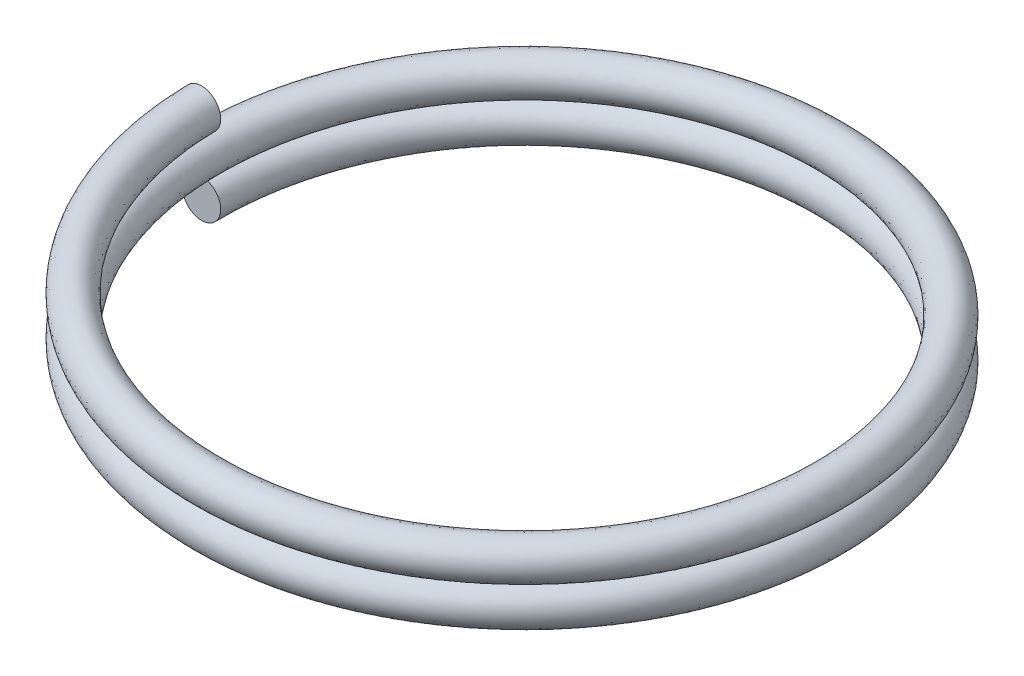
SolidWorks part; units mm, degrees
material "Stainless Steel (ferritic)"
ref_plane "Front Plane" through (0, 0, 0) normal (0, 0, 1) x (1, 0, 0)
ref_plane "Top Plane" through (0, 0, 0) normal (0, 1, 0) x (1, 0, 0)
ref_plane "Right Plane" through (0, 0, 0) normal (1, 0, 0) x (0, 0, -1)
sketch "Sketch1" plane through (0, 0, 0) normal (0, 1, 0) x (1, 0, 0)
  circle A0 centre (0, 0) radius 4.1275
  dimension "D1" = 8.255
curve "Helix/Spiral1" pitch 0.5207 height 1.0414 turns 2
sketch "Sketch2" plane through (0, 0, 0) normal (0, 0, 1) x (1, 0, 0)
  circle A0 centre (-4.1275, 0) radius 0.254
  dimension "D1" = 0.508
sweep "Sweep3" add profiles "Sketch2" path "Helix/Spiral1"
